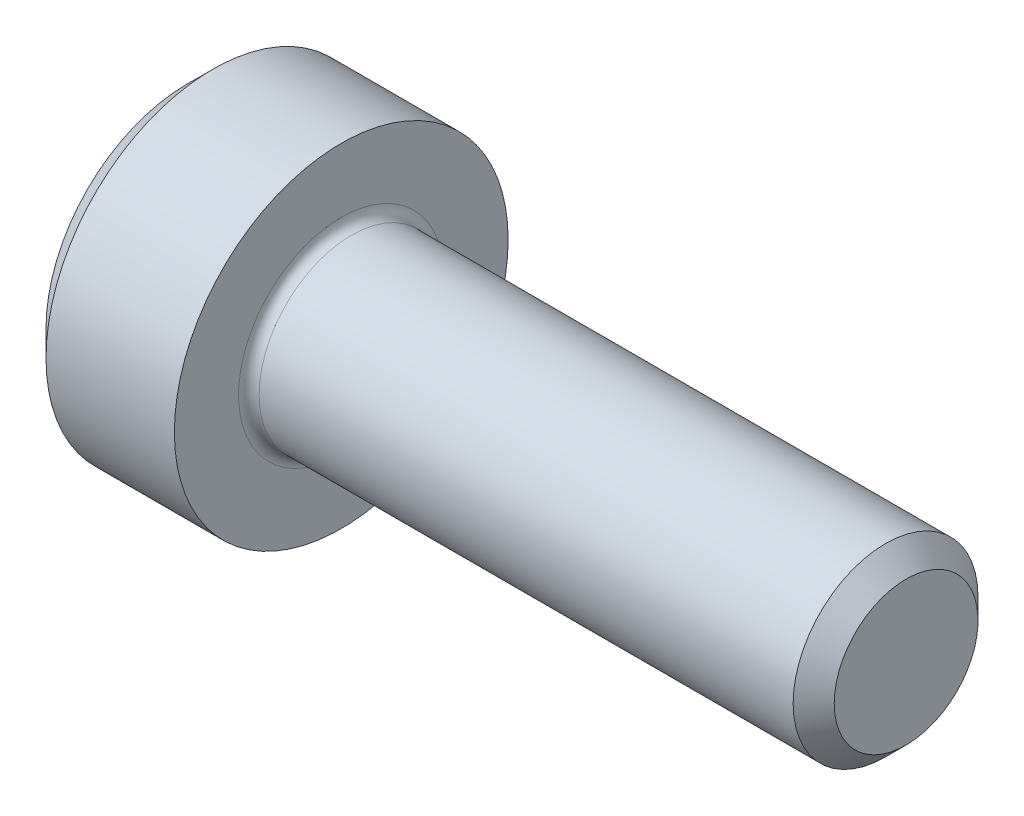
SolidWorks part; units mm, degrees
revolve "Base-Revolve" add sketch "BodySke"
sketch "BodySke" plane through (0, 0, 0) normal (0, 0, 1) x (1, 0, 0)
  line L0 (0, 0) -> (0, 2.75)
  line L1 (0.5, 3.25) -> (3, 3.25)
  line L2 (3, 3.25) -> (3, 1.8)
  line L3 (3, 1.8) -> (13.6, 1.8)
  line L4 (14, 1.4) -> (14, 0)
  line L5 (14, 0) -> (0, 0)
  line L6 (-31.75, 0) -> (127, 0) construction
  line L7 (0, 2.75) -> (0.5, 3.25)
  line L8 (14, 1.4) -> (13.6, 1.8)
  line L9 (0, -2.75) -> (0.5, -3.25) construction
  line L10 (14, -1.4) -> (13.6, -1.8) construction
  line L11 (3.8, 9.525) -> (3.8, 3.175) construction
  line L12 (6, 9.525) -> (6, 3.175) construction
  line L13 (-36, 9.525) -> (-36, 3.175) construction
  dimension "Diameter" = 3.6
  dimension "Head_ht" = 3
  dimension "Length" = 11
  dimension "Body_ch_ang" = 45
  dimension "Head_dia" = 6.5
  dimension "Head_ch_ang" = 45
  dimension "Minor_dia" = 2.8
  dimension "Advance" = 0.8
  dimension "Thread_nom" = 8
  dimension "Thread_length" = 50
  dimension "Head_ch_ht" = 0.5
cosmetic thread "ThreadCosmetic"
fillet "Fillet1" radius 0.2 1 edges at (3, 0, 1.8)
ref_plane "Plane1" through (0, 0, 0) normal (0, 0, 1) x (1, 0, 0)
ref_plane "Plane2" through (0, 0, 0) normal (0, 1, 0) x (1, 0, 0)
ref_plane "Plane3" through (0, 0, 0) normal (1, 0, 0) x (0, 0, -1)
sketch "Sketch2" plane through (0, 0, 0) normal (0, 0, 1) x (1, 0, 0)
  line L0 (0, 1.6) -> (2.5, 1.6)
  line L1 (2.5, 1.6) -> (3.4238, 0)
  line L2 (-31.75, 0) -> (127, 0) construction
  line L3 (3.4238, 0) -> (0, 0)
  line L4 (0, 0) -> (0, 1.6)
  line L5 (0, 2.75) -> (0, -2.75) construction
  line L6 (0, 0) -> (47.625, 0) construction
  line L7 (3, -3.25) -> (3, 3.25) construction
  dimension "D1" = 1.6
  dimension "D2" = 60
revolve "Hex-PreBroach" cut sketch "Sketch2" angle 360 about L6
sketch "Sketch3" plane through (0, 0, 0) normal (-1, 0, 0) x (0, 0.5, 0.866)
  line L0 (0.9238, 1.6) -> (-0.9238, 1.6)
  line L1 (-0.9238, 1.6) -> (-1.8475, 0)
  line L2 (0.9238, 1.6) -> (1.8475, 0)
  line L3 (0.9238, -1.6) -> (1.8475, 0)
  line L4 (0.9238, -1.6) -> (-0.9238, -1.6)
  line L5 (-0.9238, -1.6) -> (-1.8475, 0)
  dimension "D1" = 1.6
  dimension "D2" = 1.6
  dimension "Hex_size" = 3.2
extrude "Hex" cut sketch "Sketch3" against normal blind 2.5
sketch "Sketch4" plane through (0, 0, 0) normal (-1, 0, 0) x (0, 0, 1)
  line L0 (0, 0) -> (2.3876, 0)
  line L1 (0, 0) -> (6.1484, 3.5498) construction
  line L2 (0, 0) -> (1.1938, 2.0677)
  line L3 (1.9883, 0.576) -> (2.2704, 0.7389)
  line L4 (1.493, 1.4339) -> (1.7751, 1.5968)
  arc A0 (1.9883, 0.576) -> (1.493, 1.4339) centre (0, 0) ccw
  arc A1 (2.3876, 0) -> (2.2704, 0.7389) centre (0, 0) ccw
  arc A2 (1.1938, 2.0677) -> (1.7751, 1.5968) centre (0, 0) cw
  dimension "D1" = 30
  dimension "D2" = 60
  dimension "Spline_p_dim" = 0.9906
  dimension "D3" = 0.4953
extrude "Spline" [suppressed] cut sketch "Sketch4" against normal blind 2.5
pattern_circular "CirPattern1" [suppressed] count 6 every 60
sketch "Sketch5" plane through (0, 0, 0) normal (0, 0, 1) x (1, 0, 0)
  line L0 (-31.75, 0) -> (127, 0) construction
  line L2 (0, 2.75) -> (0, -2.75) construction
  circle A0 centre (2, 0) radius 0.675
  dimension "Drilled_hole_dia" = 1.35
  dimension "Drilled_hole_loc" = 2
extrude "Hole" [suppressed] cut sketch "Sketch5" against normal through all and the other way through all
pattern_circular "Drilled-4" [suppressed] count 2 every 60
pattern_circular "Drilled-6" [suppressed] count 3 every 60
sketch "ThdSchSke" plane through (0, 0, 0) normal (0, 0, 1) x (1, 0, 0)
  line L0 (6, -1.4) -> (5.7199, -1.8)
  line L1 (6, -1.4) -> (6.2801, -1.8)
  line L2 (6.2801, -1.8) -> (6.2801, -2.25)
  line L3 (-3.175, 0) -> (5.1513, 0) construction
  line L5 (6.2801, -2.25) -> (5.7199, -2.25)
  line L6 (5.7199, -2.25) -> (5.7199, -1.8)
  line L7 (0, 2.75) -> (0, -2.75) construction
  dimension "Thread_minor" = 2.8
  dimension "Diameter" = 3.6
  dimension "Start" = 6
revolve "ThreadSchematic" [suppressed] cut sketch "ThdSchSke" angle 360 about L3
pattern_linear "ThdSchPat" [suppressed]
equation "\"D2@Sketch3\" = \"Hex_size@Sketch3\" / 2"
equation "\"D1@Sketch3\" = \"Hex_size@Sketch3\" / 2"
equation "\"D1@Sketch2\" = \"Hex_size@Sketch3\" / 2"
equation "\"D3@Sketch4\" = \"Spline_p_dim@Sketch4\" / 2"
equation "\"Thread_minor@ThreadCosmetic\"  =  \"Minor_dia@BodySke\""
equation "\"D2@CirPattern1\" = 360 / \"Num_teeth@CirPattern1\""
equation "\"Wall_thickness@Sketch2\" = \"Head_ht@BodySke\" - \"Key_eng@Hex\""
equation "\"Thread_length@ThreadCosmetic\" = ((sgn( (\"Length@BodySke\" - \"Advance@BodySke\" ) - \"Thread_nom@BodySke\" )-1)*( (\"Length@BodySke\" - \"Advance@BodySke\" ) - \"Thread_nom@BodySke\" ))/-2+ \"Thread_nom@BodySke\""
equation "\"Thread_minor@ThdSchSke\" = \"Minor_dia@BodySke\""
equation "\"Diameter@ThdSchSke\" = \"Diameter@BodySke\""
equation "\"Overcut@ThdSchSke\" = \"Diameter@BodySke\" * 1.25"
equation "\"Start@ThdSchSke\" = \"Head_ht@BodySke\" + \"Length@BodySke\" - \"Thread_length@ThreadCosmetic\"  '---Non-countersunk---"
equation "\"Num_threads@ThdSchPat\" = int( \"Thread_length@ThreadCosmetic\" / \"Advance@BodySke\" + 0.999 )  + 1"
equation "\"Advance@ThdSchPat\" = \"Thread_length@ThreadCosmetic\" /  (\"Num_threads@ThdSchPat\" - 1) 'relax it"
equation "\"Num_threads@ThdSchPat\" = \"Num_threads@ThdSchPat\" - sgn( \"Num_threads@ThdSchPat\" - 1) '---chamfered tips only---"
